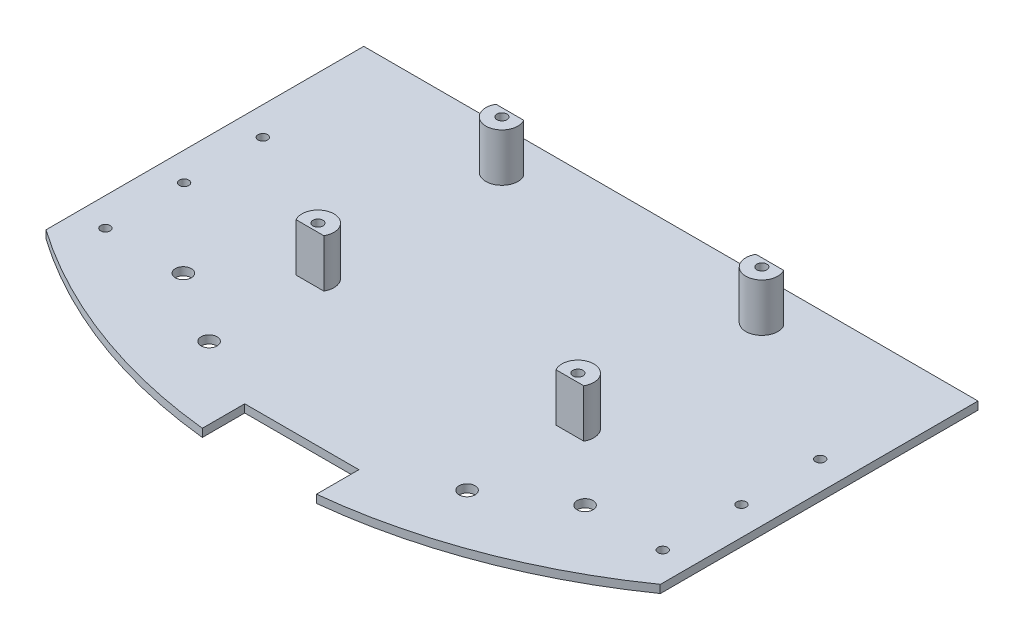
SolidWorks part; units mm, degrees
ref_plane "Front Plane" through (0, 0, 0) normal (0, 0, 1) x (1, 0, 0)
ref_plane "Top Plane" through (0, 0, 0) normal (0, 1, 0) x (1, 0, 0)
ref_plane "Right Plane" through (0, 0, 0) normal (1, 0, 0) x (0, 0, -1)
sketch "Sketch1" plane through (0, 0, 0) normal (0, 1, 0) x (1, 0, 0)
  line L1 (0, 0) -> (195.072, 0)
  line L2 (0, 0) -> (0, 152.4)
  line L3 (0, 152.4) -> (195.072, 152.4)
  line L4 (195.072, 0) -> (195.072, 152.4)
  dimension "D1" = 195.072
  dimension "D2" = 152.4
extrude "Boss-Extrude1" add sketch "Sketch1" along normal blind 2.54
sketch "Sketch2" plane through (0, 2.54, 0) normal (0, 1, 0) x (1, 0, 0)
  line L0 (0, 0) -> (195.072, 0) construction
  line L1 (79.4085, 35.1919) -> (115.6635, 35.1919)
  line L2 (79.4085, 35.1919) -> (79.4085, -11.1532)
  line L3 (79.4085, -11.1532) -> (115.6635, -11.1532)
  line L4 (115.6635, 35.1919) -> (115.6635, -11.1532)
  line L5 (97.536, 152.4) -> (97.536, 0) construction
  line L6 (195.072, 152.4) -> (0, 152.4) construction
  circle A0 centre (56.5712, 139.7) radius 1.5875
  circle A1 centre (139.1212, 139.7) radius 1.5875
  circle A2 centre (139.1212, 81.28) radius 1.5875
  circle A3 centre (56.5712, 81.28) radius 1.5875
  circle A4 centre (186, 61.35) radius 1.5
  circle A5 centre (186, 86.35) radius 1.5
  circle A6 centre (186, 111.35) radius 1.5
  circle A7 centre (9, 111.35) radius 1.5
  circle A8 centre (9, 86.35) radius 1.5
  circle A9 centre (9, 61.35) radius 1.5
  circle A10 centre (56.5712, 46.7057) radius 2.54
  circle A12 centre (33.7376, 61.35) radius 2.54
  circle A13 centre (161.3344, 61.35) radius 2.54
  circle A14 centre (138.5008, 46.7057) radius 2.54
  point P24 (97.536, -11.1532)
  point P27 (97.536, 0)
  dimension "D1" = 5.08
extrude "Cut-Extrude1" cut sketch "Sketch2" against normal up to surface (2.54 mm away) up to face at (97.536, 0, -76.2)
sketch "Sketch4" plane through (0, 2.54, 0) normal (0, 1, 0) x (1, 0, 0)
  line L0 (0, 152.4) -> (0, 0) construction
  line L1 (195.072, 0) -> (195.072, 152.4) construction
  line L2 (115.6635, 0) -> (195.072, 0) construction
  line L3 (0, 51.4886) -> (195.072, 51.4886)
  line L4 (0, 51.4886) -> (0, 0)
  line L5 (0, 0) -> (195.072, 0)
  line L6 (195.072, 51.4886) -> (195.072, 0)
  arc A1 (0, 51.4886) -> (195.072, 51.539) centre (97.5, 190.75) ccw
  point P0 (0, 51.4886)
  point P5 (195.072, 51.539)
  line M13 (115.6635, 35.1919) -> (115.6635, 0)
  line M14 (115.6635, 0) -> (195.072, 0)
  line M15 (195.072, 0) -> (195.072, 152.4)
  line M17 (0, 152.4) -> (0, 0)
  line M18 (0, 0) -> (79.4085, 0)
  line M19 (79.4085, 0) -> (79.4085, 35.1919)
extrude "Cut-Extrude2" cut sketch "Sketch4" against normal up to surface (2.54 mm away) contours A1 L3 M13 M14 M15 | A1 M17 M18 M19 up to face at (9, 0, -87.85)
sketch "Sketch6" plane through (0, 2.54, 0) normal (0, 1, 0) x (1, 0, 0)
  line L1 (52.1718, 142.24) -> (61.0517, 142.24)
  line L2 (52.1718, 142.24) -> (52.1718, 148.358)
  line L3 (52.1718, 148.358) -> (61.0517, 148.358)
  line L4 (61.0517, 142.24) -> (61.0517, 148.358)
  line L5 (143.5207, 142.24) -> (134.0412, 142.24)
  line L6 (143.5207, 142.24) -> (143.5207, 146.8177)
  line L7 (143.5207, 146.8177) -> (134.0412, 146.8177)
  line L8 (134.0412, 142.24) -> (134.0412, 146.8177)
  line L9 (143.5207, 78.74) -> (133.6113, 78.74)
  line L10 (143.5207, 78.74) -> (143.5207, 75.1717)
  line L11 (143.5207, 75.1717) -> (133.6113, 75.1717)
  line L12 (133.6113, 78.74) -> (133.6113, 75.1717)
  line L13 (52.1718, 78.74) -> (62.2493, 78.74)
  line L14 (52.1718, 78.74) -> (52.1718, 75.0088)
  line L15 (52.1718, 75.0088) -> (62.2493, 75.0088)
  line L16 (62.2493, 78.74) -> (62.2493, 75.0088)
  circle A0 centre (56.5712, 139.7) radius 5.08
  circle A1 centre (139.1212, 139.7) radius 5.08
  circle A2 centre (139.1212, 81.28) radius 5.08
  circle A3 centre (56.5712, 81.28) radius 5.08
  circle M5 centre (139.1212, 139.7) radius 1.5875
  circle M6 centre (139.1212, 81.28) radius 1.5875
  circle M7 centre (56.5712, 81.28) radius 1.5875
  circle M14 centre (56.5712, 139.7) radius 1.5875
  dimension "D1" = 10.16
extrude "Boss-Extrude2" add sketch "Sketch6" along normal blind 15.24 contours L1 A0 M14 | L5 A1 M5 | L9 A2 M6 | L13 A3 M7
